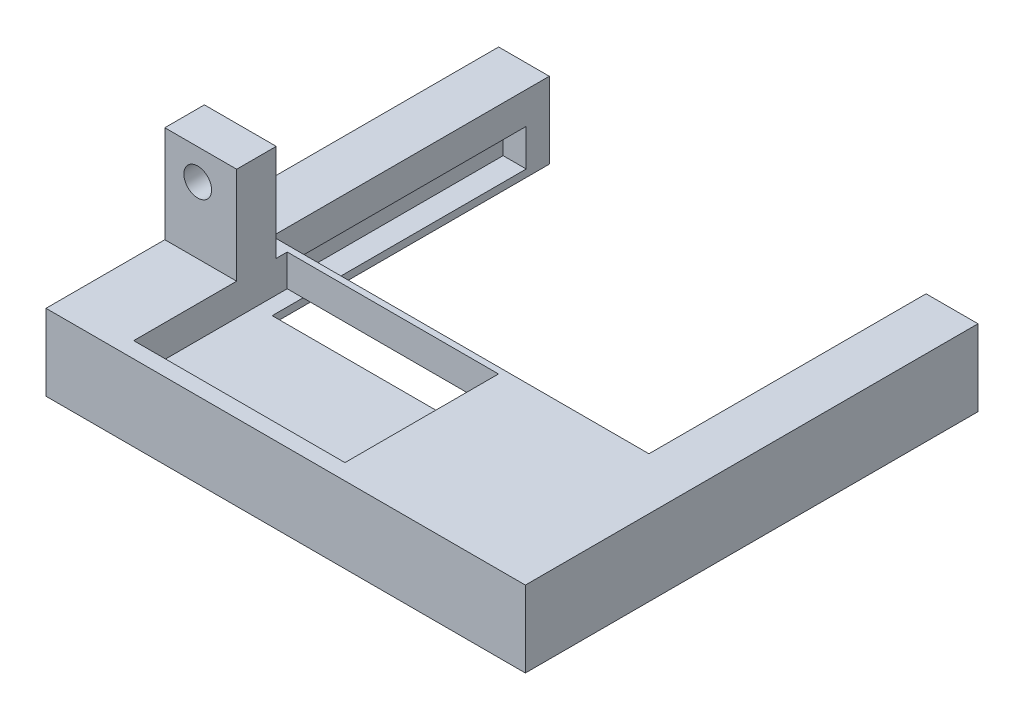
SolidWorks part; units mm, degrees
ref_plane "Front Plane" through (0, 0, 0) normal (0, 0, 1) x (1, 0, 0)
ref_plane "Top Plane" through (0, 0, 0) normal (0, 1, 0) x (1, 0, 0)
ref_plane "Right Plane" through (0, 0, 0) normal (1, 0, 0) x (0, 0, -1)
sketch "Sketch2" plane through (0, 0, 0) normal (0, 0, 1) x (1, 0, 0)
  line L1 (-53.8027, 16.2378) -> (-1.9068, 16.2378)
  line L2 (-53.8027, 16.2378) -> (-53.8027, 7.9912)
  line L3 (-53.8027, 7.9912) -> (-1.9068, 7.9912)
  line L4 (-1.9068, 16.2378) -> (-1.9068, 7.9912)
  line L5 (-53.8027, 16.2378) -> (-1.9068, 7.9912) construction
  line L6 (-53.8027, 7.9912) -> (-1.9068, 16.2378) construction
  point P0 (-6.2383, 15.5495)
extrude "Boss-Extrude1" add sketch "Sketch2" along normal blind 49
sketch "Sketch3" plane through (0, 0, 0) normal (0, 0, -1) x (-1, 0, 0)
  line L0 (1.9068, 16.2378) -> (53.8027, 16.2378) construction
  line L1 (7.527, 16.2378) -> (48.316, 16.2378)
  line L2 (7.527, 16.2378) -> (7.527, 7.9912)
  line L3 (7.527, 7.9912) -> (48.316, 7.9912)
  line L4 (48.316, 16.2378) -> (48.316, 7.9912)
  line L5 (53.8027, 7.9912) -> (1.9068, 7.9912) construction
extrude "Cut-Extrude1" cut sketch "Sketch3" against normal blind 30 contours L4 L3 L2 L1
sketch "Sketch4" plane through (0, 16.2378, 0) normal (0, 1, 0) x (1, 0, 0)
  line L1 (-46.0238, -30.6644) -> (-23.154, -30.6644)
  line L2 (-46.0238, -30.6644) -> (-46.0238, -47.2844)
  line L3 (-46.0238, -47.2844) -> (-23.154, -47.2844)
  line L4 (-23.154, -30.6644) -> (-23.154, -47.2844)
extrude "Cut-Extrude2" cut sketch "Sketch4" against normal blind 6 contours L2 L3 L4 L1
sketch "Sketch5" plane through (-7.527, 0, 0) normal (-1, 0, 0) x (0, 0, 1)
  line L0 (30, 7.9912) -> (0, 7.9912) construction
  line L1 (2.5, 12.7912) -> (30, 12.7912)
  line L2 (2.5, 12.7912) -> (2.5, 8.7912)
  line L3 (2.5, 8.7912) -> (30, 8.7912)
  line L4 (30, 12.7912) -> (30, 8.7912)
  line L5 (0, 16.2378) -> (0, 7.9912) construction
  line L6 (30, 16.2378) -> (30, 7.9912) construction
  dimension "D1" = 0.8
  dimension "D2" = 4
  dimension "D3" = 2.5
extrude "Cut-Extrude3" cut sketch "Sketch5" against normal blind 2.5
sketch "Sketch12" plane through (-48.316, 0, 0) normal (1, 0, 0) x (0, 0, -1)
  line L0 (-30, 7.9912) -> (0, 7.9912) construction
  line L1 (-2.5, 12.7912) -> (-30, 12.7912)
  line L2 (-2.5, 12.7912) -> (-2.5, 8.7912)
  line L3 (-2.5, 8.7912) -> (-30, 8.7912)
  line L4 (-30, 12.7912) -> (-30, 8.7912)
  line L5 (-30, 16.2378) -> (-30, 7.9912) construction
  line L6 (0, 16.2378) -> (0, 7.9912) construction
  dimension "D1" = 0.8
  dimension "D2" = 4
  dimension "D3" = 2.5
extrude "Cut-Extrude6" cut sketch "Sketch12" against normal blind 2.5
sketch "Sketch15" plane through (0, 0, 30) normal (0, 0, -1) x (-1, 0, 0)
  line L1 (5.027, 12.7912) -> (50.816, 12.7912)
  line L2 (5.027, 12.7912) -> (5.027, 8.7912)
  line L3 (5.027, 8.7912) -> (50.816, 8.7912)
  line L4 (50.816, 12.7912) -> (50.816, 8.7912)
extrude "Cut-Extrude7" cut sketch "Sketch15" against normal blind 17.5
sketch "Sketch17" plane through (0, 16.2378, 0) normal (0, 1, 0) x (1, 0, 0)
  line L0 (-53.8027, -49) -> (-53.8027, 0) construction
  line L1 (-53.8027, -31.8535) -> (-46.0238, -31.8535)
  line L2 (-53.8027, -31.8535) -> (-53.8027, -36.1385)
  line L3 (-53.8027, -36.1385) -> (-46.0238, -36.1385)
  line L4 (-46.0238, -31.8535) -> (-46.0238, -36.1385)
  line L5 (-46.0238, -30.6644) -> (-46.0238, -47.2844) construction
extrude "Boss-Extrude2" add sketch "Sketch17" along normal blind 10.5
sketch "Sketch18" plane through (0, 0, 36.1385) normal (0, 0, 1) x (1, 0, 0)
  circle A0 centre (-50.2396, 23.4298) radius 1.5
extrude "Cut-Extrude8" cut sketch "Sketch18" against normal blind 5 contours A0
